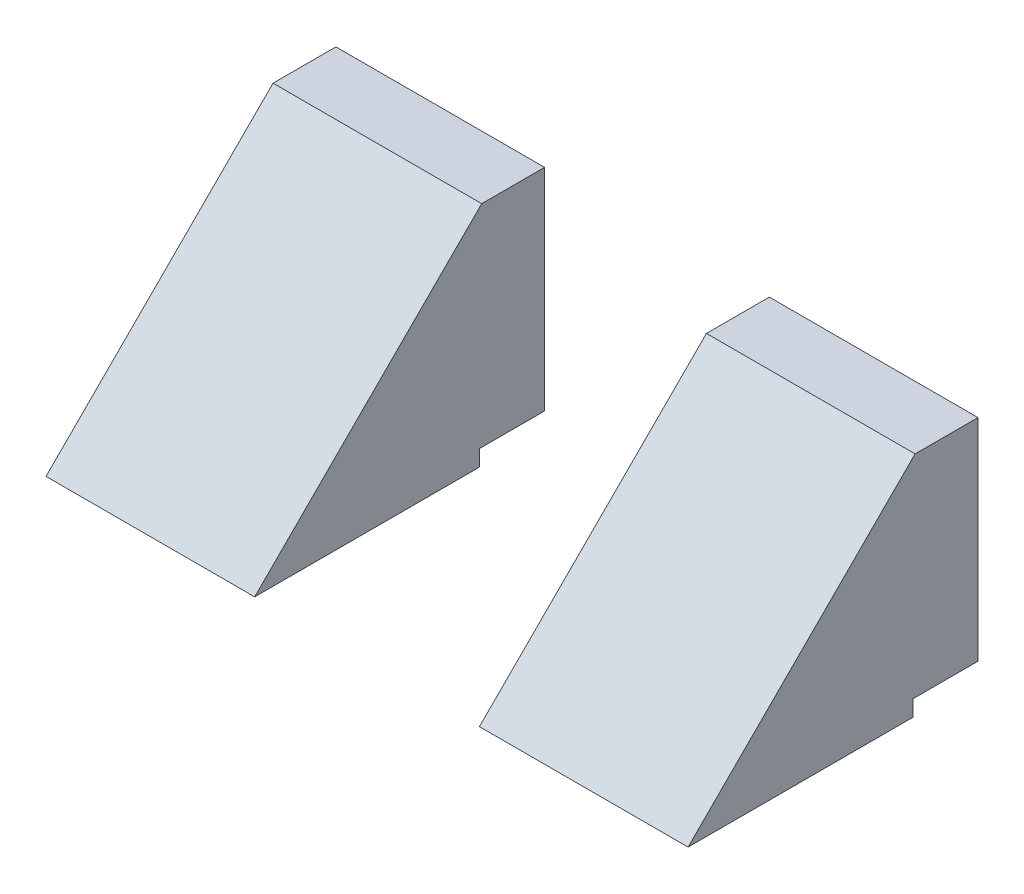
SolidWorks part; units mm, degrees
ref_plane "Front Plane" through (0, 0, 0) normal (0, 0, 1) x (1, 0, 0)
ref_plane "Top Plane" through (0, 0, 0) normal (0, 1, 0) x (1, 0, 0)
ref_plane "Right Plane" through (0, 0, 0) normal (1, 0, 0) x (0, 0, -1)
sketch "Sketch1" plane through (0, 0, 0) normal (1, 0, 0) x (0, 0, -1)
  line L0 (-1.9885, 39.9595) -> (-21.5743, 39.9595)
  line L1 (-21.5743, 39.9595) -> (-92.2885, -30.7547)
  line L2 (-92.2885, -30.7547) -> (-22.2885, -30.7547)
  line L3 (-22.2885, -30.7547) -> (-22.2885, -25.7547)
  line L4 (-22.2885, -25.7547) -> (-1.9885, -25.7547)
  line L5 (-1.9885, -25.7547) -> (-1.9885, 39.9595)
  dimension "D1" = 5
  dimension "D2" = 45
  dimension "D3" = 20.3
  dimension "D4" = 70
extrude "Boss-Extrude1" add sketch "Sketch1" along normal blind 200
sketch "Sketch2" plane through (0, 39.9595, 0) normal (0, 1, 0) x (1, 0, 0)
  line L0 (200, -1.9885) -> (0, -1.9885) construction
  line L1 (65, -1.9885) -> (135, -1.9885)
  line L2 (65, -1.9885) -> (65, -92.2885)
  line L3 (65, -92.2885) -> (135, -92.2885)
  line L4 (135, -1.9885) -> (135, -92.2885)
  line L5 (200, -92.2885) -> (0, -92.2885) construction
  line L6 (0, -21.5743) -> (0, -92.2885) construction
  line L7 (200, -21.5743) -> (200, -92.2885) construction
  dimension "D1" = 65
  dimension "D2" = 65
extrude "Cut-Extrude1" cut sketch "Sketch2" against normal blind 238
